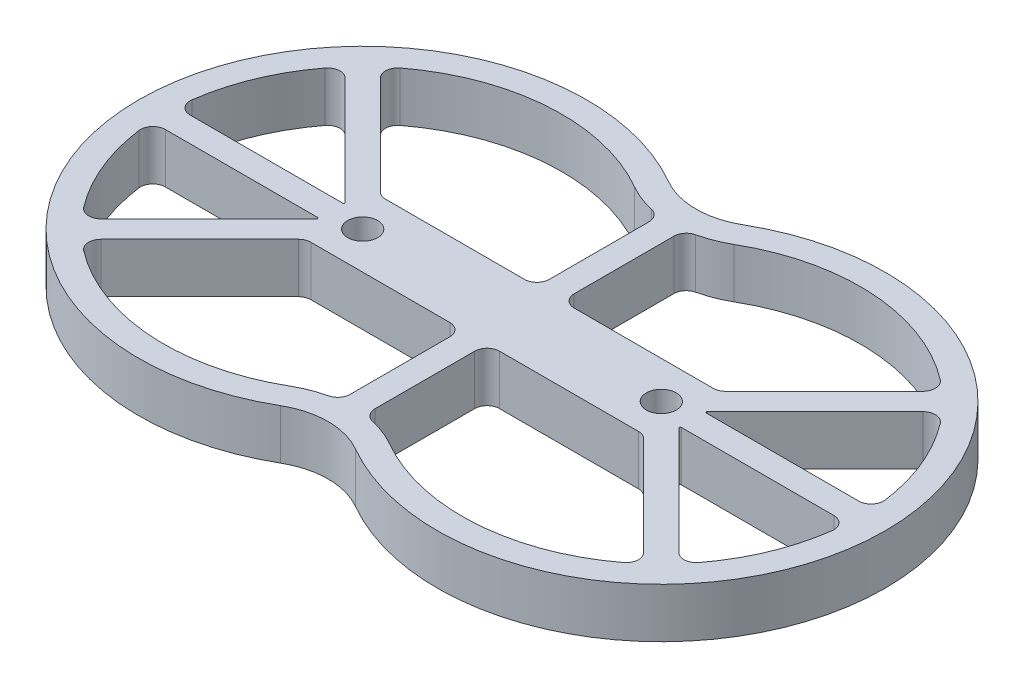
SolidWorks part; units mm, degrees
ref_plane "Front Plane" through (0, 0, 0) normal (0, 0, 1) x (1, 0, 0)
ref_plane "Top Plane" through (0, 0, 0) normal (0, 1, 0) x (1, 0, 0)
ref_plane "Right Plane" through (0, 0, 0) normal (1, 0, 0) x (0, 0, -1)
sketch "Sketch2" plane through (0, 0, 0) normal (0, 1, 0) x (1, 0, 0)
  line L0 (-150, 0) -> (150, 0) construction
  line L1 (0, 63.923) -> (0, 103.923) construction
  line L2 (60, 0) -> (123.6396, 63.6396) construction
  line L3 (5, 60.0482) -> (5, 20)
  line L4 (10, 15) -> (65.8579, 15)
  line L5 (69.3934, 16.4645) -> (109.024, 56.095)
  line L6 (0, -73.923) -> (0, 73.923) construction
  line L7 (134.3303, 5) -> (73.0368, 5)
  line L8 (72.7539, 5.6828) -> (116.095, 49.024)
  line L9 (-60, 0) -> (-123.6396, 63.6396) construction
  line L10 (-72.7539, 5.6828) -> (-116.095, 49.024)
  line L11 (-134.3303, 5) -> (-73.0368, 5)
  line L12 (-69.3934, 16.4645) -> (-109.024, 56.095)
  line L13 (-10, 15) -> (-65.8579, 15)
  line L14 (-5, 60.0482) -> (-5, 20)
  line L15 (-60, 0) -> (-123.6396, -63.6396) construction
  line L16 (60, 0) -> (123.6396, -63.6396) construction
  line L17 (0, -63.923) -> (0, -103.923) construction
  line L18 (-5, -60.0482) -> (-5, -20)
  line L19 (-10, -15) -> (-65.8579, -15)
  line L20 (-69.3934, -16.4645) -> (-109.024, -56.095)
  line L21 (-134.3303, -5) -> (-73.0368, -5)
  line L22 (-72.7539, -5.6828) -> (-116.095, -49.024)
  line L23 (72.7539, -5.6828) -> (116.095, -49.024)
  line L24 (134.3303, -5) -> (73.0368, -5)
  line L25 (69.3934, -16.4645) -> (109.024, -56.095)
  line L26 (10, -15) -> (65.8579, -15)
  line L27 (5, -60.0482) -> (5, -20)
  circle A0 centre (60, 0) radius 6
  arc A1 (139.2857, 10.6667) -> (123.6059, 48.521) centre (60, 0) ccw
  arc A2 (8.8889, 64.9232) -> (20, 69.282) centre (0, 103.923) ccw
  arc A3 (150, 0) -> (15, 77.9423) centre (60, 0) ccw
  arc A4 (0, 73.923) -> (15, 77.9423) centre (0, 103.923) ccw
  arc A5 (0, 63.923) -> (20, 69.282) centre (0, 103.923) ccw construction
  arc A6 (108.521, 63.6059) -> (20, 69.282) centre (60, 0) ccw
  arc A7 (140, 0) -> (20, 69.282) centre (60, 0) ccw construction
  arc A8 (5, 60.0482) -> (8.8889, 64.9232) centre (10, 60.0482) cw
  arc A9 (65.8579, 15) -> (69.3934, 16.4645) centre (65.8579, 20) ccw
  arc A10 (109.024, 56.095) -> (108.521, 63.6059) centre (105.4884, 59.6306) ccw
  arc A11 (116.095, 49.024) -> (123.6059, 48.521) centre (119.6306, 45.4884) cw
  arc A12 (134.3303, 5) -> (139.2857, 10.6667) centre (134.3303, 10) ccw
  arc A13 (5, 20) -> (10, 15) centre (10, 20) ccw
  arc A14 (-5, 20) -> (-10, 15) centre (-10, 20) cw
  arc A15 (-134.3303, 5) -> (-139.2857, 10.6667) centre (-134.3303, 10) cw
  arc A16 (-116.095, 49.024) -> (-123.6059, 48.521) centre (-119.6306, 45.4884) ccw
  arc A17 (-109.024, 56.095) -> (-108.521, 63.6059) centre (-105.4884, 59.6306) cw
  arc A18 (-65.8579, 15) -> (-69.3934, 16.4645) centre (-65.8579, 20) cw
  arc A19 (-5, 60.0482) -> (-8.8889, 64.9232) centre (-10, 60.0482) ccw
  arc A20 (-108.521, 63.6059) -> (-20, 69.282) centre (-60, 0) cw
  arc A21 (0, 73.923) -> (-15, 77.9423) centre (0, 103.923) cw
  arc A22 (-15, -77.9423) -> (-15, 77.9423) centre (-60, 0) cw
  arc A23 (-8.8889, 64.9232) -> (-20, 69.282) centre (0, 103.923) cw
  arc A24 (-139.2857, 10.6667) -> (-123.6059, 48.521) centre (-60, 0) cw
  circle A25 centre (-60, 0) radius 6
  arc A26 (-139.2857, -10.6667) -> (-123.6059, -48.521) centre (-60, 0) ccw
  arc A27 (-8.8889, -64.9232) -> (-20, -69.282) centre (0, -103.923) ccw
  arc A28 (0, -73.923) -> (-15, -77.9423) centre (0, -103.923) ccw
  arc A29 (-108.521, -63.6059) -> (-20, -69.282) centre (-60, 0) ccw
  arc A30 (-5, -60.0482) -> (-8.8889, -64.9232) centre (-10, -60.0482) cw
  arc A31 (-65.8579, -15) -> (-69.3934, -16.4645) centre (-65.8579, -20) ccw
  arc A32 (-109.024, -56.095) -> (-108.521, -63.6059) centre (-105.4884, -59.6306) ccw
  arc A33 (-116.095, -49.024) -> (-123.6059, -48.521) centre (-119.6306, -45.4884) cw
  arc A34 (-134.3303, -5) -> (-139.2857, -10.6667) centre (-134.3303, -10) ccw
  arc A35 (-5, -20) -> (-10, -15) centre (-10, -20) ccw
  arc A36 (5, -20) -> (10, -15) centre (10, -20) cw
  arc A37 (134.3303, -5) -> (139.2857, -10.6667) centre (134.3303, -10) cw
  arc A38 (116.095, -49.024) -> (123.6059, -48.521) centre (119.6306, -45.4884) ccw
  arc A39 (109.024, -56.095) -> (108.521, -63.6059) centre (105.4884, -59.6306) cw
  arc A40 (65.8579, -15) -> (69.3934, -16.4645) centre (65.8579, -20) cw
  arc A41 (5, -60.0482) -> (8.8889, -64.9232) centre (10, -60.0482) ccw
  arc A42 (108.521, -63.6059) -> (20, -69.282) centre (60, 0) cw
  arc A43 (0, -73.923) -> (15, -77.9423) centre (0, -103.923) cw
  arc A44 (150, 0) -> (15, -77.9423) centre (60, 0) cw
  arc A45 (8.8889, -64.9232) -> (20, -69.282) centre (0, -103.923) cw
  arc A46 (139.2857, -10.6667) -> (123.6059, -48.521) centre (60, 0) cw
  arc A47 (-72.7539, 5.6828) -> (-73.0368, 5) centre (-73.0368, 5.4) cw
  arc A48 (73.0368, 5) -> (72.7539, 5.6828) centre (73.0368, 5.4) cw
  arc A49 (72.7539, -5.6828) -> (73.0368, -5) centre (73.0368, -5.4) cw
  arc A50 (-73.0368, -5) -> (-72.7539, -5.6828) centre (-73.0368, -5.4) cw
  point P1 (123.6059, 63.6733)
  point P5 (132.5664, 72.5664)
  point P7 (0, -83.923)
  point P8 (5, 40.0241)
  point P11 (142.4871, 82.4871)
  point P32 (112.9224, 59.9935)
  point P37 (0, 0)
  point P67 (-112.9224, 59.9935)
  point P70 (0, 0)
  point P116 (-112.9224, -59.9935)
  point P117 (112.9224, -59.9935)
  point P118 (152.0419, 0)
  point P119 (-72.0711, 5)
  point P122 (72.0711, 5)
  point P125 (72.0711, -5)
  point P128 (-72.0711, -5)
  dimension "D3" = 12
  dimension "D4" = 80
  dimension "D5" = 80
  dimension "D12" = 5
  dimension "D13" = 5
  dimension "D14" = 5
  dimension "D15" = 5
  dimension "D16" = 5
  dimension "D17" = 5
  dimension "D18" = 0.4
  dimension "D19" = 0.4
  dimension "D1" = 60
  dimension "D2" = 45
  dimension "D7" = 5
  dimension "D8" = 15
  dimension "D9" = 5
  dimension "D10" = 5
  dimension "D11" = 5
  dimension "D6" = 10
extrude "Boss-Extrude1" add sketch "Sketch2" along normal blind 20
